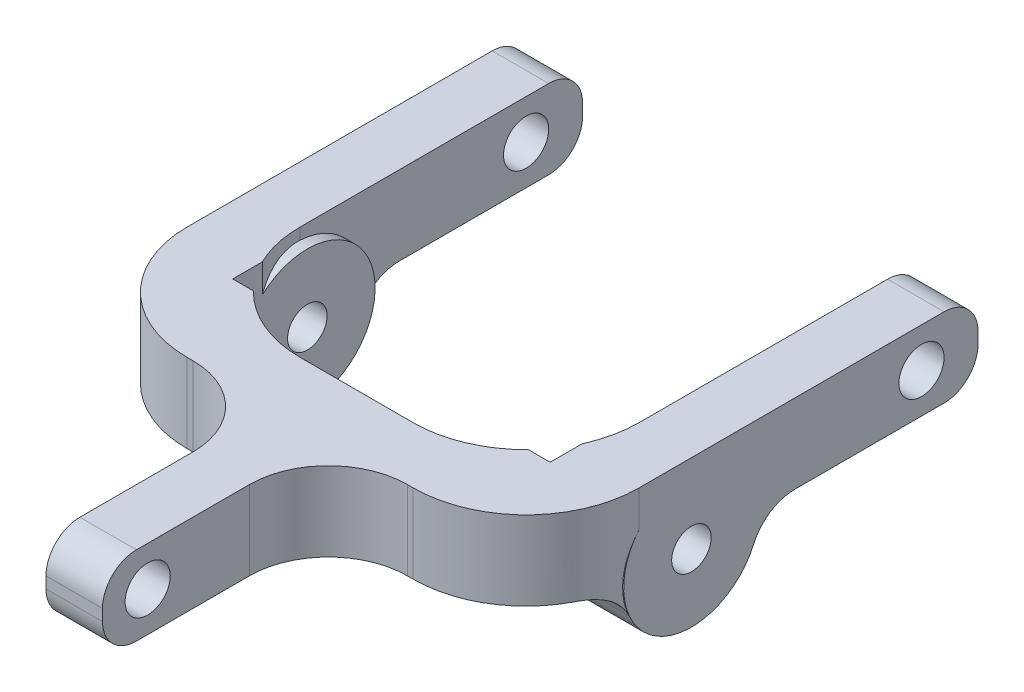
SolidWorks part; units mm, degrees
ref_plane "Front Plane" through (0, 0, 0) normal (0, 0, 1) x (1, 0, 0)
ref_plane "Top Plane" through (0, 0, 0) normal (0, 1, 0) x (1, 0, 0)
ref_plane "Right Plane" through (0, 0, 0) normal (1, 0, 0) x (0, 0, -1)
sketch "Sketch1" plane through (0, 0, 0) normal (1, 0, 0) x (0, 0, -1)
  line L1 (-20, 3.5) -> (20, 3.5)
  line L2 (-20, 3.5) -> (-20, -3.5)
  line L3 (-20, -3.5) -> (20, -3.5)
  line L4 (20, 3.5) -> (20, -3.5)
  line L5 (-20, 3.5) -> (20, -3.5) construction
  line L6 (-20, -3.5) -> (20, 3.5) construction
  point P0 (0, 0)
  dimension "D1" = 7
  dimension "D2" = 40
extrude "Boss-Extrude1" add sketch "Sketch1" along normal blind 40
sketch "Sketch2" plane through (0, 3.5, 0) normal (0, 1, 0) x (1, 0, 0)
  line L0 (40, 20) -> (0, 20) construction
  line L1 (5, 20) -> (35, 20)
  line L2 (5, 20) -> (5, -5)
  line L3 (15, -15) -> (25, -15)
  line L4 (35, 20) -> (35, -5)
  line L5 (0, 20) -> (0, -20) construction
  line L6 (40, 20) -> (40, -20) construction
  arc A0 (25, -15) -> (35, -5) centre (25, -5) ccw
  arc A1 (5, -5) -> (15, -15) centre (15, -5) ccw
  point P14 (5, -15)
  dimension "D4" = 10
  dimension "D1" = 5
  dimension "D2" = 5
  dimension "D3" = 35
extrude "Cut-Extrude1" cut sketch "Sketch2" against normal through all
fillet "Fillet1" radius 10 2 edges at (40, 0, 20) (0, 0, 20)
sketch "Sketch5" plane through (0, 0, 20) normal (0, 0, 1) x (1, 0, 0)
  line L0 (30, 3.5) -> (10, 3.5) construction
  line L1 (17.5, 3.5) -> (22.5, 3.5)
  line L2 (17.5, 3.5) -> (17.5, -3.5)
  line L3 (17.5, -3.5) -> (22.5, -3.5)
  line L4 (22.5, 3.5) -> (22.5, -3.5)
  line L5 (30, -3.5) -> (10, -3.5) construction
  line L6 (20, 3.5) -> (20, -3.5) construction
  point P10 (20, -3.5)
  dimension "D1" = 5
extrude "Boss-Extrude2" add sketch "Sketch5" along normal blind 20
fillet "Fillet2" radius 7 2 edges at (22.5, 0, 20) (17.5, 0, 20)
fillet "Fillet3" radius 3 6 edges at (2.5, -3.5, -20) (2.5, 3.5, -20) (37.5, -3.5, -20) (37.5, 3.5, -20) (20, -3.5, 40) (20, 3.5, 40)
sketch "Sketch6" plane through (40, 0, 0) normal (1, 0, 0) x (0, 0, -1)
  line L0 (15, 0) -> (0, 0) construction
  circle A0 centre (15, 0) radius 2
  dimension "D1" = 15
extrude "Cut-Extrude2" cut sketch "Sketch6" against normal through all
sketch "Sketch7" plane through (22.5, 0, 0) normal (1, 0, 0) x (0, 0, -1)
  line L0 (0, 0) -> (-36, 0) construction
  circle A0 centre (-36, 0) radius 2
  dimension "D1" = 36
extrude "Cut-Extrude3" cut sketch "Sketch7" against normal through all
sketch "Sketch8" plane through (40, 0, 0) normal (1, 0, 0) x (0, 0, -1)
  line L0 (-10, -3.5) -> (17, -3.5) construction
  circle A0 centre (-5.366, -3.5) radius 6
extrude "Boss-Extrude3" add sketch "Sketch8" against normal blind 40
sketch "Sketch9" plane through (0, 0, 0) normal (0, 1, 0) x (1, 0, 0)
  line L1 (5.9985, -11.972) -> (34.1001, -11.972)
  line L2 (5.9985, -11.972) -> (5.9985, 2.2267)
  line L3 (5.9985, 2.2267) -> (34.1001, 2.2267)
  line L4 (34.1001, -11.972) -> (34.1001, 2.2267)
extrude "Cut-Extrude4" cut sketch "Sketch9" against normal through all and the other way through all
sketch "Sketch10" plane through (40, 0, 0) normal (1, 0, 0) x (0, 0, -1)
  circle A0 centre (-5.366, -3.5) radius 1.75
  dimension "D1" = 3.5
extrude "Cut-Extrude5" cut sketch "Sketch10" against normal through all
fillet "Fillet4" radius 4 8 edges at (37.5, -3.5, -0.634) (2.5, -3.5, -0.634) (3.0461, -3.5, 11.366) (37.0032, -3.5, 11.366) (33.1344, -3.5, 11.972) (6.9149, -3.5, 11.972) (5.9985, -3.5, 11.669) (34.1001, -3.5, 11.669)
